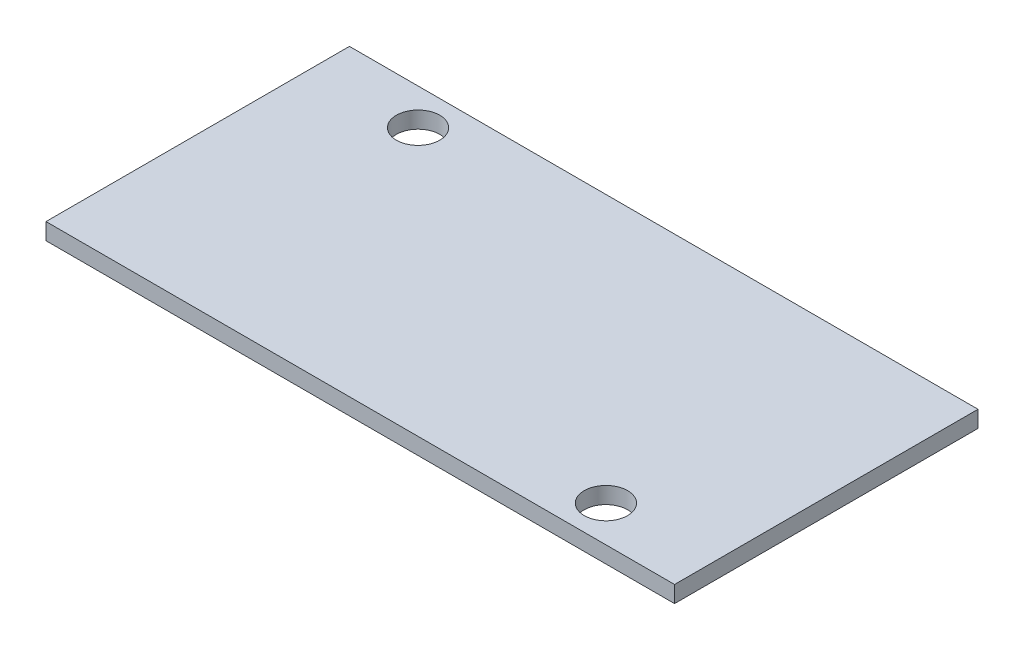
SolidWorks part; units mm, degrees
ref_plane "Front Plane" through (0, 0, 0) normal (0, 0, 1) x (1, 0, 0)
ref_plane "Top Plane" through (0, 0, 0) normal (0, 1, 0) x (1, 0, 0)
ref_plane "Right Plane" through (0, 0, 0) normal (1, 0, 0) x (0, 0, -1)
sketch "Sketch1" plane through (0, 0, 0) normal (0, 1, 0) x (1, 0, 0)
  line L1 (-21.75, -10.5) -> (21.75, -10.5)
  line L2 (-21.75, -10.5) -> (-21.75, 10.5)
  line L3 (-21.75, 10.5) -> (21.75, 10.5)
  line L4 (21.75, -10.5) -> (21.75, 10.5)
  line L5 (-21.75, -10.5) -> (21.75, 10.5) construction
  line L6 (-21.75, 10.5) -> (21.75, -10.5) construction
  circle A0 centre (-14.5, 8) radius 1.5
  circle A1 centre (14.5, -8) radius 1.5
  point P0 (0, 0)
  dimension "D5" = 3
  dimension "D1" = 43.5
  dimension "D2" = 21
  dimension "D3" = 7.25
  dimension "D4" = 7.25
  dimension "D6" = 2.5
  dimension "D7" = 2.5
extrude "Boss-Extrude1" add sketch "Sketch1" along normal blind 1.15
